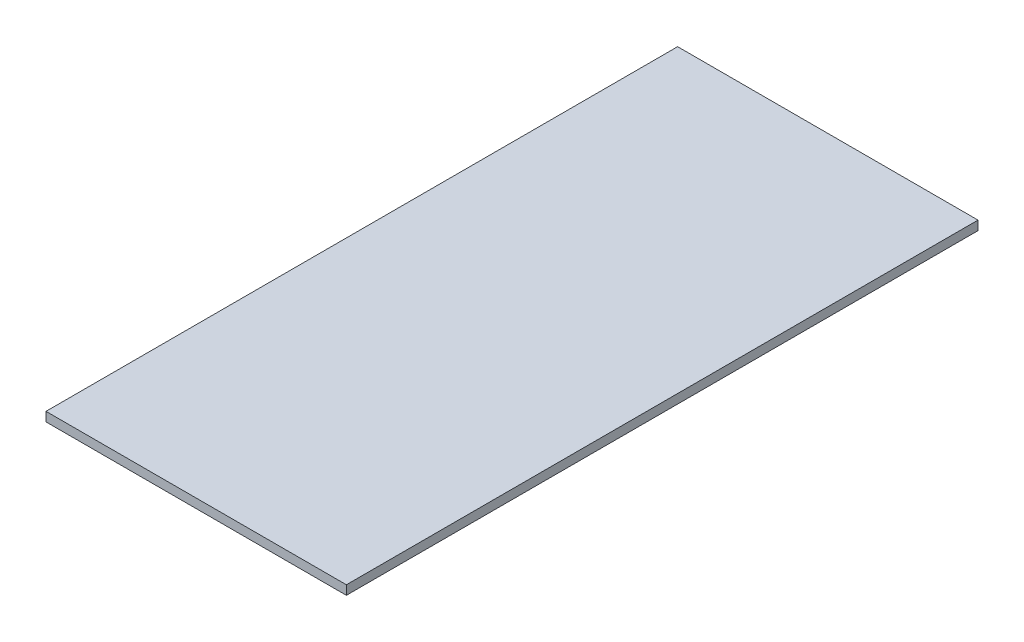
SolidWorks part; units mm, degrees
ref_plane "Front Plane" through (0, 0, 0) normal (0, 0, 1) x (1, 0, 0)
ref_plane "Top Plane" through (0, 0, 0) normal (0, 1, 0) x (1, 0, 0)
ref_plane "Right Plane" through (0, 0, 0) normal (1, 0, 0) x (0, 0, -1)
sketch "Sketch1" plane through (0, 0, 0) normal (0, 1, 0) x (1, 0, 0)
  line L1 (-270.637, -569.087) -> (270.637, -569.087)
  line L2 (-270.637, -569.087) -> (-270.637, 569.087)
  line L3 (-270.637, 569.087) -> (270.637, 569.087)
  line L4 (270.637, -569.087) -> (270.637, 569.087)
  line L5 (-270.637, -569.087) -> (270.637, 569.087) construction
  line L6 (-270.637, 569.087) -> (270.637, -569.087) construction
  point P0 (0, 0)
  dimension "D1" = 541.274
  dimension "D2" = 1138.174
extrude "Boss-Extrude1" add sketch "Sketch1" along normal blind 16.51
